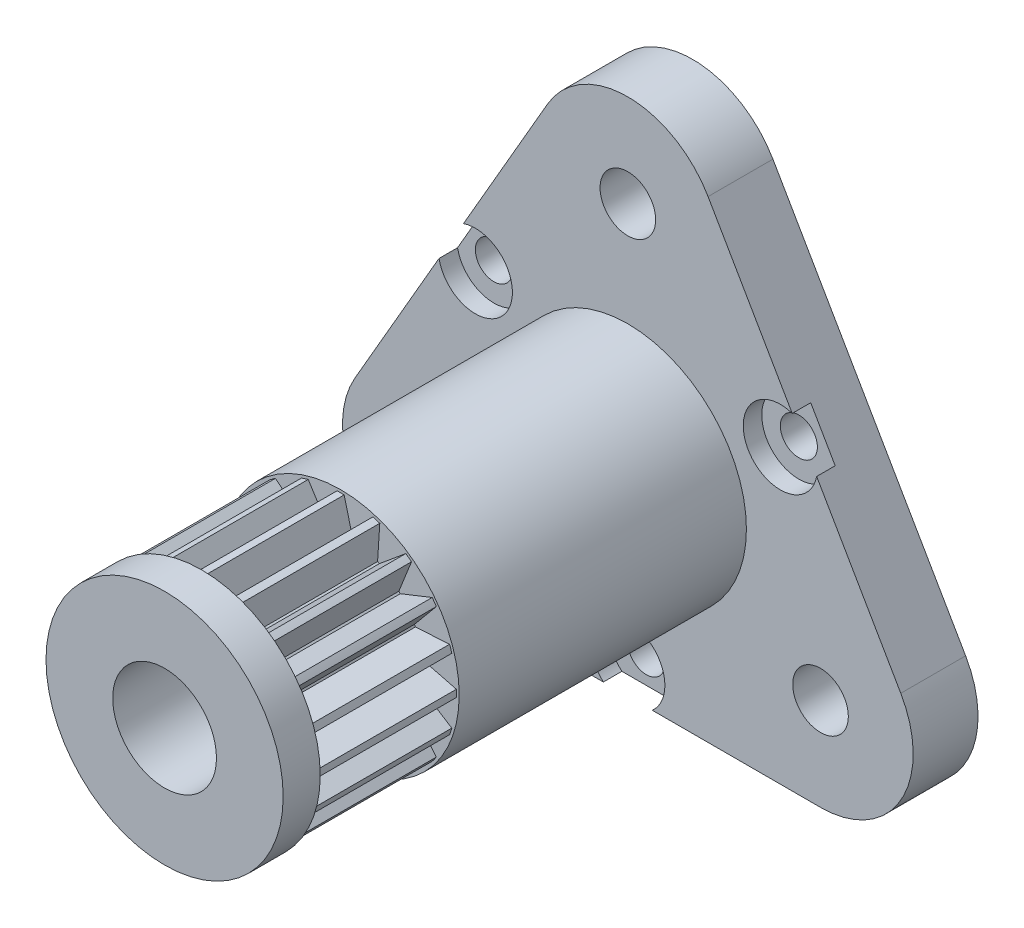
SolidWorks part; units mm, degrees
ref_plane "Front Plane" through (0, 0, 0) normal (0, 0, 1) x (1, 0, 0)
ref_plane "Top Plane" through (0, 0, 0) normal (0, 1, 0) x (1, 0, 0)
ref_plane "Right Plane" through (0, 0, 0) normal (1, 0, 0) x (0, 0, -1)
sketch "Sketch1" plane through (0, 0, 0) normal (0, 0, 1) x (1, 0, 0)
  line L0 (0, 12.0089) -> (0, 0) construction
  line L1 (0, 0) -> (-10.4, -6.0044) construction
  line L2 (0, 0) -> (10.4, -6.0044) construction
  line L3 (-14.7301, -3.5044) -> (-4.3301, 14.5089)
  line L4 (4.3301, 14.5089) -> (14.7301, -3.5044)
  line L5 (10.4, -11.0044) -> (-10.4, -11.0044)
  line L6 (7.5274, 4.346) -> (9.5301, 5.5022) construction
  line L7 (-5.1962, 3) -> (-7.5274, 4.346) construction
  line L8 (-7.5274, 4.346) -> (-9.5301, 5.5022) construction
  line L9 (0, -8.6919) -> (0, -11.0044) construction
  line L10 (0, 12.0089) -> (10.4, -6.0044) construction
  line L11 (10.4, -6.0044) -> (-10.4, -6.0044) construction
  line L12 (-10.4, -6.0044) -> (0, 12.0089) construction
  circle A0 centre (0, 12.0089) radius 1.5
  circle A1 centre (-10.4, -6.0044) radius 1.5
  circle A2 centre (10.4, -6.0044) radius 1.5
  arc A4 (4.3301, 14.5089) -> (-4.3301, 14.5089) centre (0, 12.0089) ccw
  arc A5 (-14.7301, -3.5044) -> (-10.4, -11.0044) centre (-10.4, -6.0044) ccw
  arc A6 (10.4, -11.0044) -> (14.7301, -3.5044) centre (10.4, -6.0044) ccw
  circle A7 centre (0, 0) radius 6 construction
  spline S0 degree 3 poles (12.0715, -6.9088) (-10.7674, -6.2165) (0.0526, 13.9086) (12.0715, -6.9088) (-10.7674, -6.2165) (0.0526, 13.9086) knots -1 -0.674106 -0.325894 0 0.325894 0.674106 1 1.325894 1.674106 2 only from (-5.2828, -3.05) to (-5.2828, -3.05) construction
  point P38 (0, 0)
  dimension "D4" = 3
  dimension "D5" = 12
  dimension "D6" = 10
  dimension "D1" = 20.8
  dimension "D2" = 120
  dimension "D3" = 120
  dimension "D9" = 3
extrude "Boss-Extrude1" add sketch "Sketch1" along normal blind 3.5
sketch "Sketch2" plane through (0, 0, 3.5) normal (0, 0, 1) x (1, 0, 0)
  line L0 (-10.4, -6.0044) -> (0, 0) construction
  line L1 (0, 0) -> (0, 12.0089) construction
  line L2 (0, 0) -> (10.4, -6.0044) construction
  circle A0 centre (0, 0) radius 6.4
  dimension "D2" = 12.8
extrude "Boss-Extrude2" add sketch "Sketch2" along normal blind 25
sketch "Sketch3" plane through (0, 0, 28.5) normal (0, 0, 1) x (1, 0, 0)
  circle A0 centre (0, 0) radius 2.8
  dimension "D1" = 5.6
extrude "Cut-Extrude1" cut sketch "Sketch3" against normal through all
ref_plane "Plane1" through (0, 0, 26.5) normal (0, 0, 1) x (1, 0, 0)
sketch "Sketch6" plane through (0, 0, 26.5) normal (0, 0, 1) x (1, 0, 0)
  line L0 (4.5, 0) -> (7, 0) construction
  line L1 (7, 0) -> (4.4528, 0.65)
  line L2 (7, 0) -> (4.4528, -0.65)
  line L3 (6.6574, -2.1631) -> (4.034, -1.9942)
  line L4 (6.6574, -2.1631) -> (4.4357, -0.7578)
  line L5 (5.6631, -4.1145) -> (3.2203, -3.1432)
  line L6 (5.6631, -4.1145) -> (3.9845, -2.0914)
  line L7 (4.1145, -5.6631) -> (2.0914, -3.9845)
  line L8 (4.1145, -5.6631) -> (3.1432, -3.2203)
  line L9 (2.1631, -6.6574) -> (0.7578, -4.4357)
  line L10 (2.1631, -6.6574) -> (1.9942, -4.034)
  line L11 (0, -7) -> (-0.65, -4.4528)
  line L12 (0, -7) -> (0.65, -4.4528)
  line L13 (-2.1631, -6.6574) -> (-1.9942, -4.034)
  line L14 (-2.1631, -6.6574) -> (-0.7578, -4.4357)
  line L15 (-4.1145, -5.6631) -> (-3.1432, -3.2203)
  line L16 (-4.1145, -5.6631) -> (-2.0914, -3.9845)
  line L17 (-5.6631, -4.1145) -> (-3.9845, -2.0914)
  line L18 (-5.6631, -4.1145) -> (-3.2203, -3.1432)
  line L19 (-6.6574, -2.1631) -> (-4.4357, -0.7578)
  line L20 (-6.6574, -2.1631) -> (-4.034, -1.9942)
  line L21 (-7, 0) -> (-4.4528, 0.65)
  line L22 (-7, 0) -> (-4.4528, -0.65)
  line L23 (-6.6574, 2.1631) -> (-4.034, 1.9942)
  line L24 (-6.6574, 2.1631) -> (-4.4357, 0.7578)
  line L25 (-5.6631, 4.1145) -> (-3.2203, 3.1432)
  line L26 (-5.6631, 4.1145) -> (-3.9845, 2.0914)
  line L27 (-4.1145, 5.6631) -> (-2.0914, 3.9845)
  line L28 (-4.1145, 5.6631) -> (-3.1432, 3.2203)
  line L29 (-2.1631, 6.6574) -> (-0.7578, 4.4357)
  line L30 (-2.1631, 6.6574) -> (-1.9942, 4.034)
  line L31 (0, 7) -> (0.65, 4.4528)
  line L32 (0, 7) -> (-0.65, 4.4528)
  line L33 (2.1631, 6.6574) -> (1.9942, 4.034)
  line L34 (2.1631, 6.6574) -> (0.7578, 4.4357)
  line L35 (4.1145, 5.6631) -> (3.1432, 3.2203)
  line L36 (4.1145, 5.6631) -> (2.0914, 3.9845)
  line L37 (5.6631, 4.1145) -> (3.9845, 2.0914)
  line L38 (5.6631, 4.1145) -> (3.2203, 3.1432)
  line L39 (6.6574, 2.1631) -> (4.4357, 0.7578)
  line L40 (6.6574, 2.1631) -> (4.034, 1.9942)
  line L41 (4.4357, 0.7578) -> (4.4528, 0.65)
  line L42 (4.4528, -0.65) -> (4.4357, -0.7578)
  line L43 (4.034, -1.9942) -> (3.9845, -2.0914)
  line L44 (3.2203, -3.1432) -> (3.1432, -3.2203)
  line L45 (2.0914, -3.9845) -> (1.9942, -4.034)
  line L46 (0.7578, -4.4357) -> (0.65, -4.4528)
  line L47 (-0.65, -4.4528) -> (-0.7578, -4.4357)
  line L48 (-1.9942, -4.034) -> (-2.0914, -3.9845)
  line L49 (-3.1432, -3.2203) -> (-3.2203, -3.1432)
  line L50 (-3.9845, -2.0914) -> (-4.034, -1.9942)
  line L51 (-4.4357, -0.7578) -> (-4.4528, -0.65)
  line L52 (-4.4528, 0.65) -> (-4.4357, 0.7578)
  line L53 (-4.034, 1.9942) -> (-3.9845, 2.0914)
  line L54 (-3.2203, 3.1432) -> (-3.1432, 3.2203)
  line L55 (-2.0914, 3.9845) -> (-1.9942, 4.034)
  line L56 (-0.7578, 4.4357) -> (-0.65, 4.4528)
  line L57 (0.65, 4.4528) -> (0.7578, 4.4357)
  line L58 (1.9942, 4.034) -> (2.0914, 3.9845)
  line L59 (3.1432, 3.2203) -> (3.2203, 3.1432)
  line L60 (3.9845, 2.0914) -> (4.034, 1.9942)
  circle A0 centre (0, 0) radius 4.5 construction
  circle A1 centre (0, 0) radius 7 construction
  circle A2 centre (0, 0) radius 9.5696
  point P67 (0, 0)
  point P106 (0, 0)
  dimension "D1" = 9
  dimension "D6" = 14
  dimension "D2" = 0.65
  dimension "D3" = 0.65
  dimension "D5" = 20
  dimension "D4" = 20
extrude "Cut-Extrude6" cut sketch "Sketch6" against normal blind 7.5
sketch "Sketch7" plane through (0, 0, 26.5) normal (0, 0, 1) x (1, 0, 0)
  circle A0 centre (0, 0) radius 6.25
  circle A1 centre (0, 0) radius 17.7758
  dimension "D1" = 12.5
extrude "Cut-Extrude7" cut sketch "Sketch7" against normal blind 7.5
sketch "Sketch8" plane through (0, 0, 3.5) normal (0, 0, 1) x (1, 0, 0)
  line L0 (9.5301, 5.5022) -> (6.9282, 4) construction
  line L2 (14.7301, -3.5044) -> (4.3301, 14.5089) construction
  circle A0 centre (0, 0) radius 8 construction
  circle A10 centre (0, 0) radius 8 construction
  circle A14 centre (8.2292, 4.7511) radius 1
  circle A15 centre (0, -9.5022) radius 1
  circle A16 centre (-8.2292, 4.7511) radius 1
  point P16 (0, 0)
  dimension "D2" = 2
  dimension "D3" = 3
  dimension "D1" = 16
extrude "Cut-Extrude8" cut sketch "Sketch8" against normal through all
sketch "Sketch9" plane through (0, 0, 3.5) normal (0, 0, 1) x (1, 0, 0)
  circle A15 centre (8.2292, 4.7511) radius 2
  circle A16 centre (0, -9.5022) radius 2
  circle A17 centre (-8.2292, 4.7511) radius 2
  point P8 (0, 0)
  dimension "D1" = 4
  dimension "D2" = 3
extrude "Cut-Extrude9" cut sketch "Sketch9" against normal blind 1 and the other way blind 13
